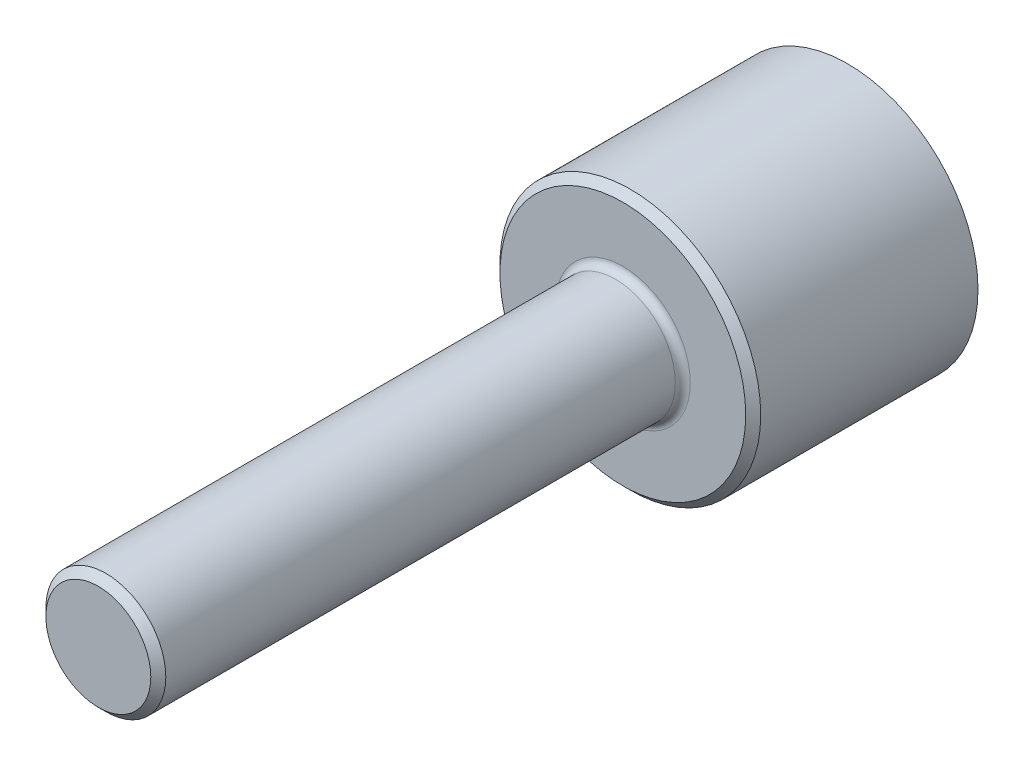
SolidWorks part; units mm, degrees
material "AISI 304"
ref_plane "Front Plane" through (0, 0, 0) normal (0, 0, 1) x (1, 0, 0)
ref_plane "Top Plane" through (0, 0, 0) normal (0, 1, 0) x (1, 0, 0)
ref_plane "Right Plane" through (0, 0, 0) normal (1, 0, 0) x (0, 0, -1)
sketch "Sketch1" plane through (0, 0, 0) normal (0, 0, 1) x (1, 0, 0)
  circle A0 centre (0, 0) radius 17.4
  dimension "D1" = 34.8
extrude "Body" add sketch "Sketch1" along normal blind 30
sketch "Sketch2" plane through (0, 0, 30) normal (0, 0, 1) x (1, 0, 0)
  circle A0 centre (0, 0) radius 8
  dimension "D1" = 16
extrude "Spigot" add sketch "Sketch2" along normal blind 70
chamfer "Chamfers" distance 1 angle 45 2 edges at (8, 0, 100) (17.4, 0, 30)
fillet "Fillet" radius 1 1 edges at (8, 0, 30)
